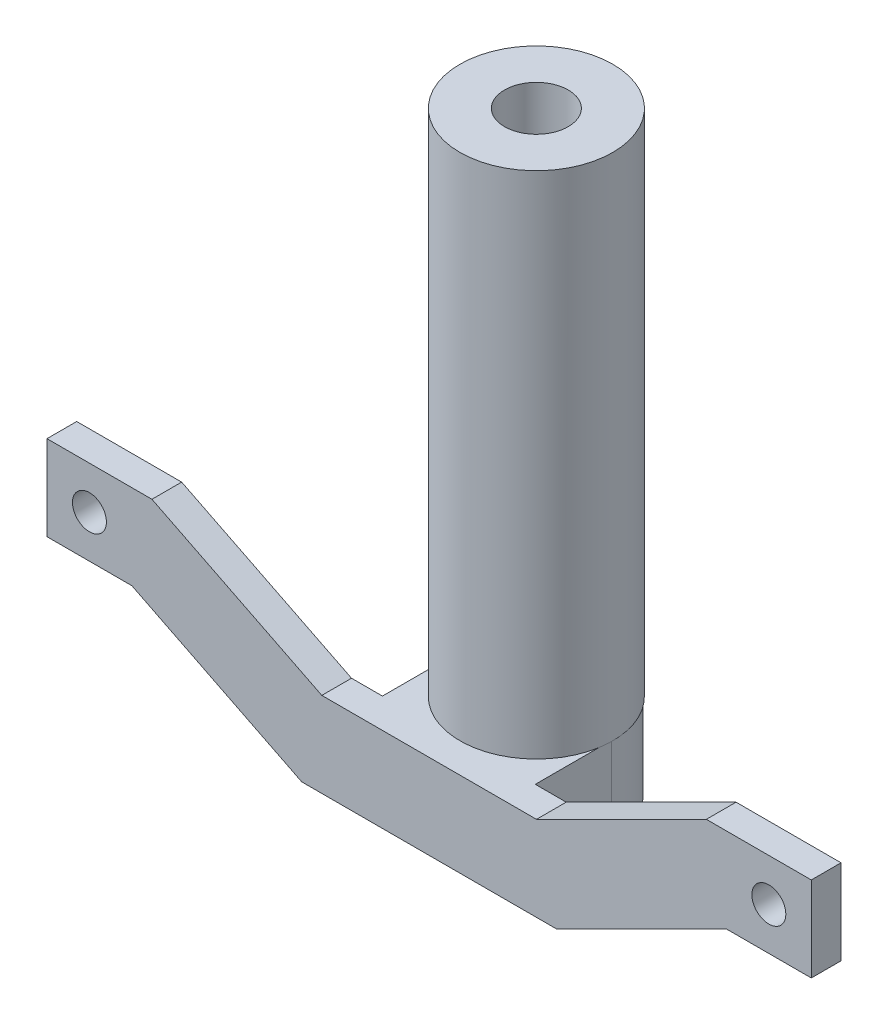
SolidWorks part; units mm, degrees
ref_plane "前视基准面" through (0, 0, 0) normal (0, 0, 1) x (1, 0, 0)
ref_plane "上视基准面" through (0, 0, 0) normal (0, 1, 0) x (1, 0, 0)
ref_plane "右视基准面" through (0, 0, 0) normal (1, 0, 0) x (0, 0, -1)
sketch "草图1" plane through (0, 0, 0) normal (0, 0, 1) x (1, 0, 0)
  line L0 (-30, 0) -> (30, 0)
  line L1 (30, 0) -> (70, 20)
  line L2 (70, 20) -> (90, 20)
  line L3 (90, 20) -> (90, 40)
  line L4 (90, 40) -> (65.2786, 40)
  line L5 (65.2786, 40) -> (25.2786, 20)
  line L6 (25.2786, 20) -> (-25.2786, 20)
  line L7 (0, 0) -> (0, 20) construction
  line L8 (-65.2786, 40) -> (-25.2786, 20)
  line L9 (-90, 40) -> (-65.2786, 40)
  line L10 (-90, 20) -> (-90, 40)
  line L11 (-70, 20) -> (-90, 20)
  line L12 (-30, 0) -> (-70, 20)
  circle A0 centre (80, 30) radius 4
  circle A1 centre (-80, 30) radius 4
  point P12 (90, 30)
  dimension "D8" = 8
  dimension "D1" = 20
  dimension "D2" = 20
  dimension "D3" = 20
  dimension "D4" = 90
  dimension "D5" = 20
  dimension "D6" = 30
  dimension "D7" = 20
  dimension "D9" = 10
extrude "凸台-拉伸1" add sketch "草图1" along normal blind 7
sketch "草图2" plane through (0, 0, 0) normal (0, 0, -1) x (-1, 0, 0)
  line L0 (-18, 0) -> (-18, 20)
  line L1 (-18, 0) -> (18, 0)
  line L2 (-18, 20) -> (18, 20)
  line L3 (18, 0) -> (18, 20)
  line L4 (30, 0) -> (-30, 0) construction
  line L5 (-25.2786, 20) -> (25.2786, 20) construction
  dimension "D1" = 36
extrude "凸台-拉伸2" add sketch "草图2" along normal blind 36
sketch "草图3" plane through (0, 20, 0) normal (0, 1, 0) x (1, 0, 0)
  line L0 (18, 36) -> (-18, 0) construction
  line L1 (18, 18) -> (18, 36)
  line L2 (18, 36) -> (-18, 36)
  line L3 (-18, 36) -> (-18, 18)
  circle A0 centre (0, 18) radius 18
  circle A2 centre (0.2554, 18) radius 7.5
  line M9 (18, 0) -> (18, 36)
  line M10 (18, 36) -> (-18, 36)
  line M11 (-18, 36) -> (-18, 0)
  dimension "D1" = 36
  dimension "D2" = 15
extrude "切除-拉伸2" cut sketch "草图3" against normal blind 36 contours A2 L0 | L0 A2 | L0 A0 M9 | L0 A0 M10 | A0 L2 M11
sketch "草图4" plane through (0, 20, 0) normal (0, 1, 0) x (1, 0, 0)
  circle A0 centre (0.2554, 18) radius 18
  circle A1 centre (0.2554, 18) radius 7.5
  dimension "D1" = 36
  dimension "D2" = 15
extrude "凸台-拉伸3" add sketch "草图4" along normal blind 120
